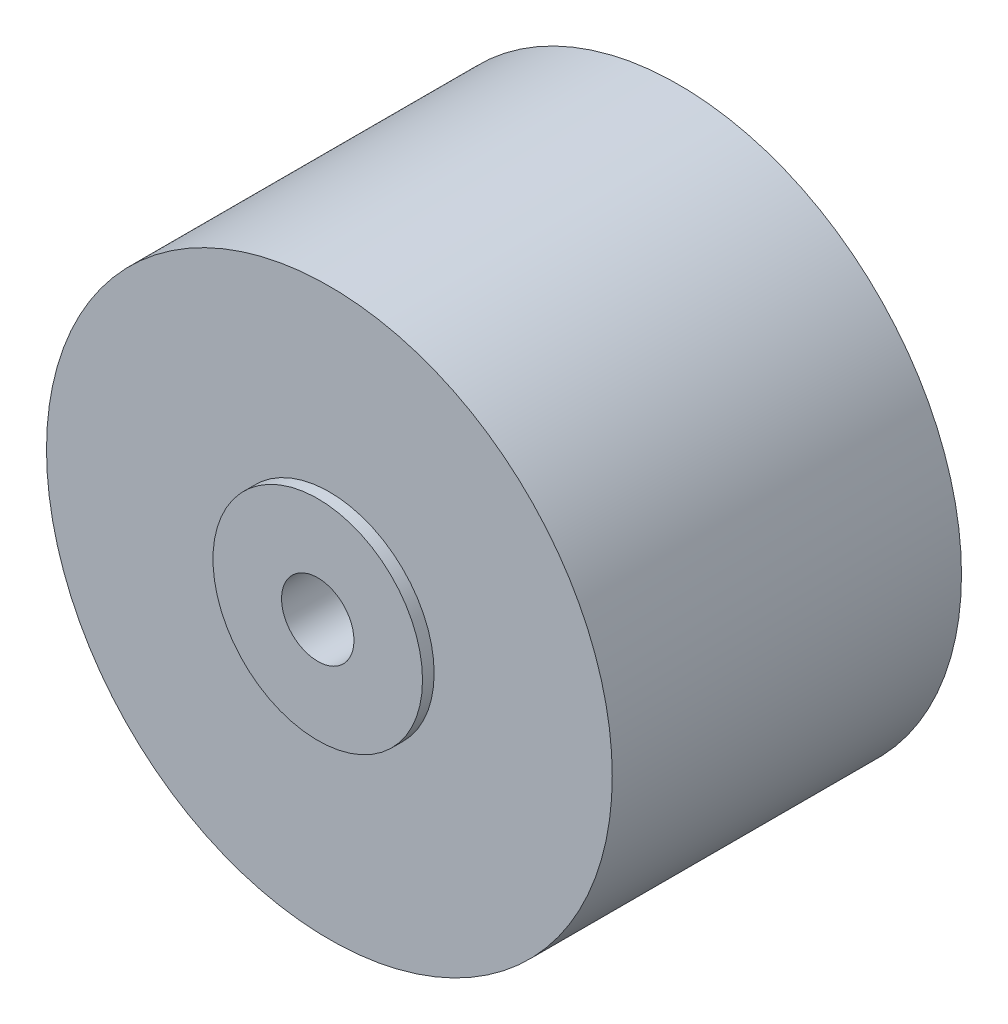
SolidWorks part; units mm, degrees
ref_plane "Plano frontal" through (0, 0, 0) normal (0, 0, 1) x (1, 0, 0)
ref_plane "Plano superior" through (0, 0, 0) normal (0, 1, 0) x (1, 0, 0)
ref_plane "Plano direito" through (0, 0, 0) normal (1, 0, 0) x (0, 0, -1)
sketch "Esboço1" plane through (0, 0, 0) normal (0, 0, 1) x (1, 0, 0)
  circle A0 centre (0, 0) radius 12.15
  dimension "D1" = 24.3
extrude "Ressalto-extrusão1" add sketch "Esboço1" along normal blind 15
sketch "Esboço2" plane through (0, 0, 0) normal (0, 0, 1) x (1, 0, 0)
  line L0 (-12.15, 0) -> (12.15, 0) construction
  line L1 (12.15, 0) -> (0, 12.15) construction
  line L2 (0, 12.15) -> (0, -12.15) construction
  circle A0 centre (0, 0) radius 12.15 construction
  circle A1 centre (0, 0) radius 4.5
  dimension "D1" = 9
extrude "Ressalto-extrusão2" add sketch "Esboço2" along normal blind 15.5
sketch "Esboço3" plane through (0, 0, 0) normal (0, 0, 1) x (1, 0, 0)
  circle A0 centre (0, 0) radius 1.555
  dimension "D1" = 3.11
extrude "Corte-extrusão1" cut sketch "Esboço3" against normal blind 15.5 and the other way blind 19.5
